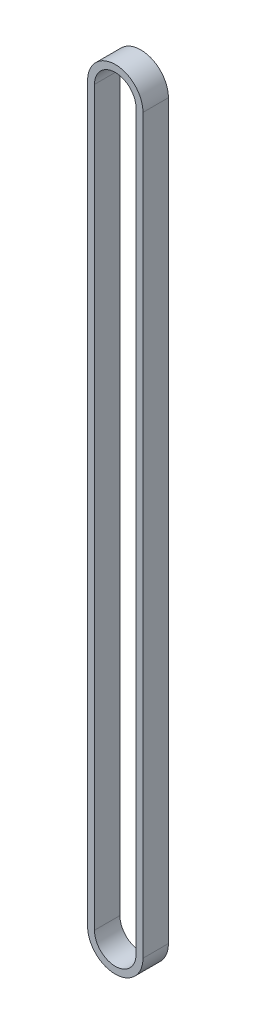
SolidWorks part; units mm, degrees
material "Резина"
ref_plane "Спереди" through (0, 0, 0) normal (0, 0, 1) x (1, 0, 0)
ref_plane "Сверху" through (0, 0, 0) normal (0, 1, 0) x (1, 0, 0)
ref_plane "Справа" through (0, 0, 0) normal (1, 0, 0) x (0, 0, -1)
sketch "Эскиз1" plane through (0, 0, 0) normal (0, 0, 1) x (1, 0, 0)
  line L0 (0, 0) -> (0, 213) construction
  line L1 (-8.05, 213) -> (-8.05, 0)
  line L2 (-6.05, 0) -> (-6.05, 213)
  line L3 (6.05, 0) -> (6.05, 213)
  line L4 (8.05, 213) -> (8.05, 0)
  arc A0 (-6.05, 0) -> (6.05, 0) centre (0, 0) ccw
  arc A1 (6.05, 213) -> (-6.05, 213) centre (0, 213) ccw
  arc A2 (8.05, 213) -> (-8.05, 213) centre (0, 213) ccw
  arc A3 (-8.05, 0) -> (8.05, 0) centre (0, 0) ccw
  dimension "D1" = 12.1
  dimension "D2" = 213
  dimension "D3" = 2
extrude "Бобышка-Вытянуть1" add sketch "Эскиз1" along normal blind 7.4
